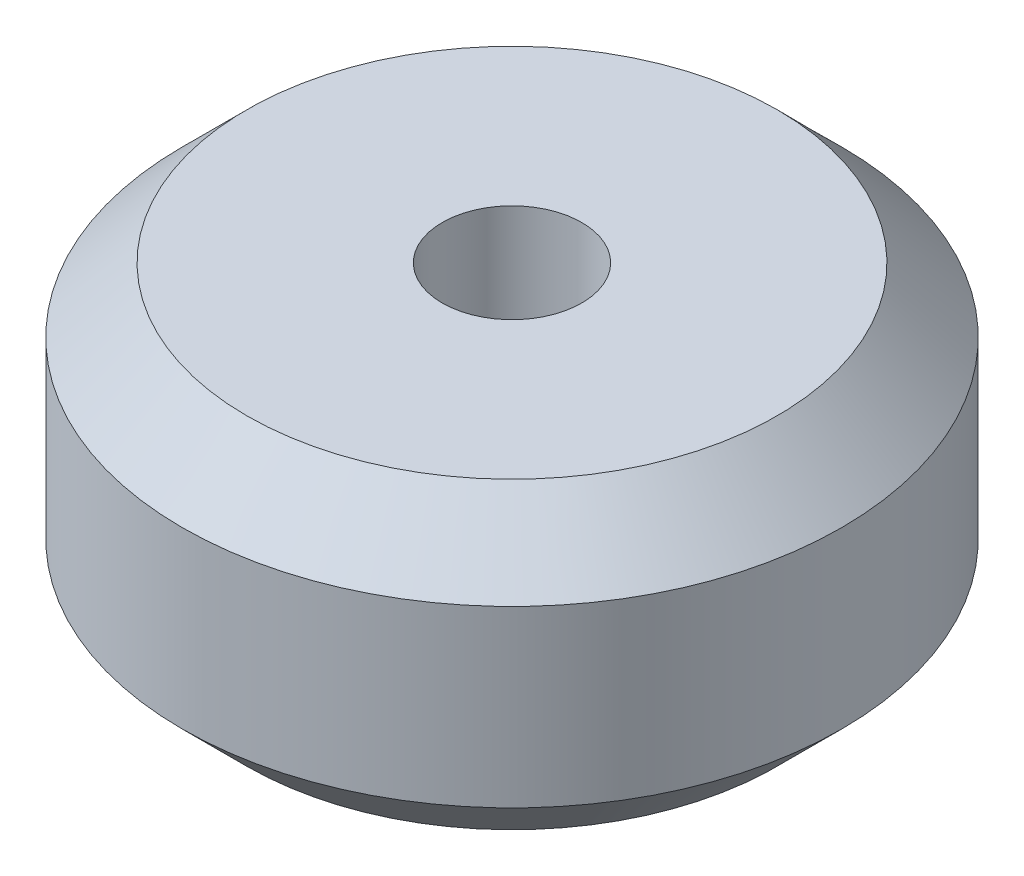
SolidWorks part; units mm, degrees
material "POLYURETHANE (11671)"
ref_plane "Front Plane" through (0, 0, 0) normal (0, 0, 1) x (1, 0, 0)
ref_plane "Top Plane" through (0, 0, 0) normal (0, 1, 0) x (1, 0, 0)
ref_plane "Right Plane" through (0, 0, 0) normal (1, 0, 0) x (0, 0, -1)
sketch "Sketch1" plane through (0, 0, 0) normal (0, 0, 1) x (1, 0, 0)
  line L0 (0, 5.5245) -> (2.54, 5.5245) construction
  line L1 (2.54, 5.5245) -> (2.54, -5.5245)
  line L2 (2.54, -5.5245) -> (9.652, -5.5245)
  line L3 (9.652, -5.5245) -> (12.0015, -3.175)
  line L4 (12.0015, -3.175) -> (12.0015, 3.175)
  line L5 (12.0015, 3.175) -> (9.652, 5.5245)
  line L6 (9.652, 5.5245) -> (2.54, 5.5245)
  line L7 (0, 5.5245) -> (0, -5.5245) construction
  point P4 (12.0015, 0)
  point P10 (0, 0)
  dimension "D1" = 2.54
  dimension "D2" = 11.049
  dimension "D3" = 12.0015
  dimension "D4" = 6.35
revolve "Revolve1" add sketch "Sketch1" angle 360 about L7
